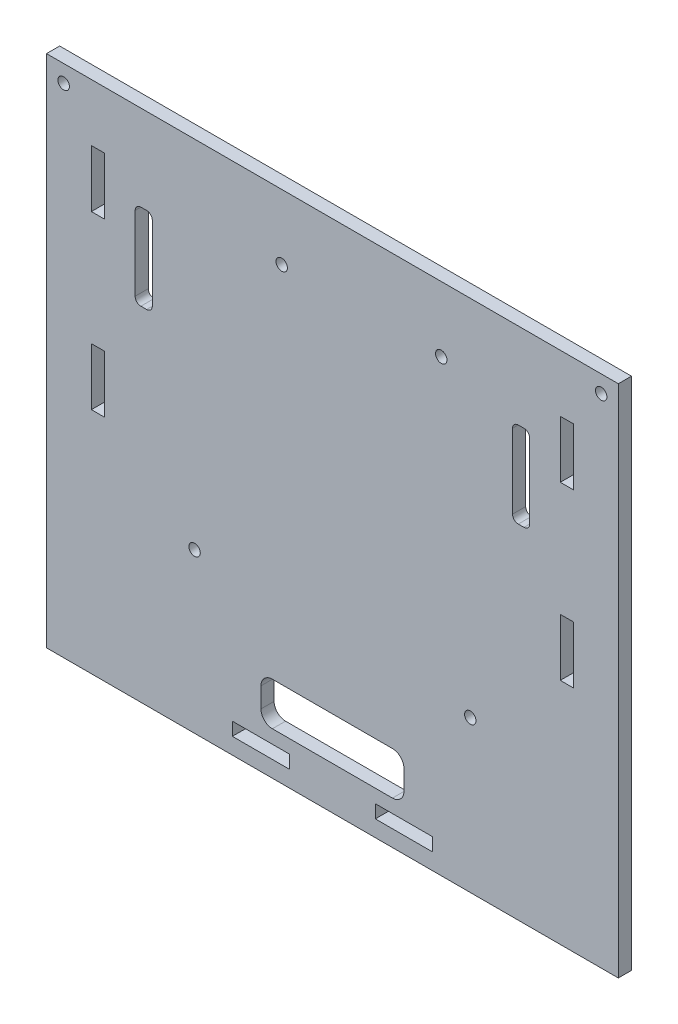
SolidWorks part; units mm, degrees
ref_plane "Front Plane" through (0, 0, 0) normal (0, 0, 1) x (1, 0, 0)
ref_plane "Top Plane" through (0, 0, 0) normal (0, 1, 0) x (1, 0, 0)
ref_plane "Right Plane" through (0, 0, 0) normal (1, 0, 0) x (0, 0, -1)
sketch "Sketch1" plane through (0, 0, 0) normal (0, 0, 1) x (1, 0, 0)
  line L0 (0, -57) -> (0, -90)
  line L1 (0, 0) -> (100, 0)
  line L2 (0, 0) -> (0, -57)
  line L3 (0, -90) -> (23, -90)
  line L4 (100, 0) -> (100, -57)
  line L5 (77, -90) -> (100, -90)
  line L6 (100, -90) -> (100, -57)
  line L7 (0, -57) -> (23, -57) construction
  line L8 (23, -90) -> (23, -57) construction
  line L11 (100, -57) -> (77, -57) construction
  line L12 (77, -90) -> (77, -57) construction
  line L14 (23, -90) -> (77, -90)
  dimension "D1" = 100
  dimension "D2" = 57
  dimension "D3" = 23
  dimension "D4" = 23
  dimension "D5" = 33
  dimension "D6" = 33
  dimension "D7" = 54
extrude "Boss-Extrude1" add sketch "Sketch1" along normal blind 2.3
sketch "Sketch7" plane through (0, 0, 2.3) normal (0, 0, 1) x (1, 0, 0)
  line L0 (100, -90) -> (100, 0) construction
  line L1 (67.5, -84.85) -> (100, -84.85) construction
  line L2 (100, -90) -> (100, 0) construction
  line L3 (89.85, -10) -> (92.15, -10)
  line L4 (89.85, -10) -> (89.85, -20)
  line L5 (89.85, -20) -> (92.15, -20)
  line L6 (92.15, -10) -> (92.15, -20)
  line L7 (89.85, -10) -> (92.15, -20) construction
  line L8 (89.85, -20) -> (92.15, -10) construction
  line L9 (100, 0) -> (0, 0) construction
  line L10 (89.85, -40) -> (92.15, -50) construction
  line L11 (92.15, -40) -> (92.15, -50)
  line L12 (89.85, -40) -> (89.85, -50)
  line L13 (89.85, -50) -> (92.15, -40) construction
  line L14 (89.85, -40) -> (92.15, -40)
  line L15 (89.85, -50) -> (92.15, -50)
  line L16 (7.85, -10) -> (10.15, -10)
  line L17 (7.85, -20) -> (10.15, -10) construction
  line L18 (7.85, -10) -> (7.85, -20)
  line L19 (7.85, -20) -> (10.15, -20)
  line L20 (10.15, -10) -> (10.15, -20)
  line L21 (7.85, -10) -> (10.15, -20) construction
  line L22 (0, 0) -> (0, -90) construction
  line L23 (7.85, -50) -> (10.15, -40) construction
  line L24 (10.15, -40) -> (10.15, -50)
  line L25 (7.85, -50) -> (10.15, -50)
  line L26 (7.85, -40) -> (10.15, -50) construction
  line L27 (7.85, -40) -> (7.85, -50)
  line L28 (7.85, -40) -> (10.15, -40)
  line L29 (0, -90) -> (100, -90) construction
  line L30 (32.5, -87.15) -> (42.5, -87.15)
  line L31 (32.5, -87.15) -> (32.5, -84.85)
  line L32 (32.5, -84.85) -> (42.5, -84.85)
  line L33 (42.5, -87.15) -> (42.5, -84.85)
  line L34 (32.5, -87.15) -> (42.5, -84.85) construction
  line L35 (32.5, -84.85) -> (42.5, -87.15) construction
  line L36 (67.5, -87.15) -> (57.5, -87.15)
  line L37 (67.5, -87.15) -> (67.5, -84.85)
  line L38 (67.5, -84.85) -> (57.5, -84.85)
  line L39 (57.5, -87.15) -> (57.5, -84.85)
  line L40 (67.5, -87.15) -> (57.5, -84.85) construction
  line L41 (67.5, -84.85) -> (57.5, -87.15) construction
  point P0 (91, -15)
  point P7 (9, -15)
  point P11 (91, -45)
  point P21 (9, -45)
  point P26 (37.5, -86)
  point P31 (62.5, -86)
  dimension "D1" = 2.3
  dimension "D2" = 10
  dimension "D3" = 9
  dimension "D4" = 10
  dimension "D5" = 10
  dimension "D6" = 9
  dimension "D7" = 20
  dimension "D8" = 10
  dimension "D9" = 9
  dimension "D10" = 10
  dimension "D11" = 9
  dimension "D12" = 20
  dimension "D13" = 2.3
  dimension "D14" = 2.3
  dimension "D15" = 10
  dimension "D16" = 2.3
  dimension "D17" = 4
  dimension "D18" = 4
  dimension "D19" = 10
  dimension "D20" = 10
  dimension "D21" = 2.3
  dimension "D22" = 2.3
  dimension "D23" = 15
  dimension "D24" = 32.5
extrude "Cut-Extrude2" cut sketch "Sketch7" against normal through all
sketch "Sketch9" plane through (0, 0, 2.3) normal (0, 0, 1) x (1, 0, 0)
  line L0 (100, 0) -> (0, 0) construction
  line L1 (0, 0) -> (0, -90) construction
  line L2 (100, -90) -> (100, 0) construction
  line L4 (0, -90) -> (100, -90) construction
  line L6 (25.89, -62.2) -> (0, -62.2) construction
  line L7 (0, 0) -> (0, -90) construction
  line L8 (74.11, -63.5) -> (100, -63.5) construction
  line L9 (100, -90) -> (100, 0) construction
  circle A0 centre (3, -3) radius 1
  circle A1 centre (97, -3) radius 1
  circle A2 centre (41.13, -11.4) radius 1
  circle A3 centre (69.03, -11.4) radius 1
  circle A4 centre (25.89, -62.2) radius 1
  circle A5 centre (74.11, -63.5) radius 1
  dimension "D1" = 3
  dimension "D3" = 2
  dimension "D4" = 3
  dimension "D6" = 2
  dimension "D7" = 11.4
  dimension "D10" = 2
  dimension "D12" = 2
  dimension "D13" = 25.89
  dimension "D17" = 2
  dimension "D18" = 2
  dimension "D2" = 3
  dimension "D5" = 3
  dimension "D8" = 11.4
  dimension "D9" = 41.13
  dimension "D11" = 30.97
  dimension "D14" = 26.5
  dimension "D15" = 25.89
  dimension "D16" = 27.8
extrude "Cut-Extrude4" cut sketch "Sketch9" against normal through all
sketch "Sketch10" plane through (0, 0, 2.3) normal (0, 0, 1) x (1, 0, 0)
  line L0 (100, 0) -> (0, 0) construction
  line L1 (15.5, -15) -> (18.5, -15)
  line L2 (15.5, -15) -> (15.5, -30)
  line L3 (15.5, -30) -> (18.5, -30)
  line L4 (18.5, -15) -> (18.5, -30)
  line L5 (0, 0) -> (0, -90) construction
  line L6 (100, -90) -> (100, 0) construction
  line L7 (81.5, -15) -> (84.5, -15)
  line L8 (81.5, -15) -> (81.5, -30)
  line L9 (81.5, -30) -> (84.5, -30)
  line L10 (84.5, -15) -> (84.5, -30)
  line L12 (37.5, -75) -> (62.5, -75)
  line L13 (37.5, -75) -> (37.5, -82.5)
  line L14 (37.5, -82.5) -> (62.5, -82.5)
  line L15 (62.5, -75) -> (62.5, -82.5)
  line L16 (0, -90) -> (100, -90) construction
  line L17 (62.5, -75) -> (100, -75) construction
  line L18 (100, -90) -> (100, 0) construction
  dimension "D1" = 3
  dimension "D2" = 15
  dimension "D3" = 15
  dimension "D4" = 15.5
  dimension "D5" = 3
  dimension "D6" = 15
  dimension "D7" = 15.5
  dimension "D8" = 15
  dimension "D9" = 25
  dimension "D10" = 7.5
  dimension "D11" = 37.5
  dimension "D12" = 7.5
extrude "Cut-Extrude5" cut sketch "Sketch10" against normal through all
fillet "Fillet2" radius 1 8 edges at (84.5, -30, 1.15) (81.5, -30, 1.15) (81.5, -15, 1.15) (84.5, -15, 1.15) (18.5, -30, 1.15) (18.5, -15, 1.15) (15.5, -15, 1.15) (15.5, -30, 1.15)
fillet "Fillet3" radius 2 4 edges at (62.5, -82.5, 1.15) (62.5, -75, 1.15) (37.5, -82.5, 1.15) (37.5, -75, 1.15)
